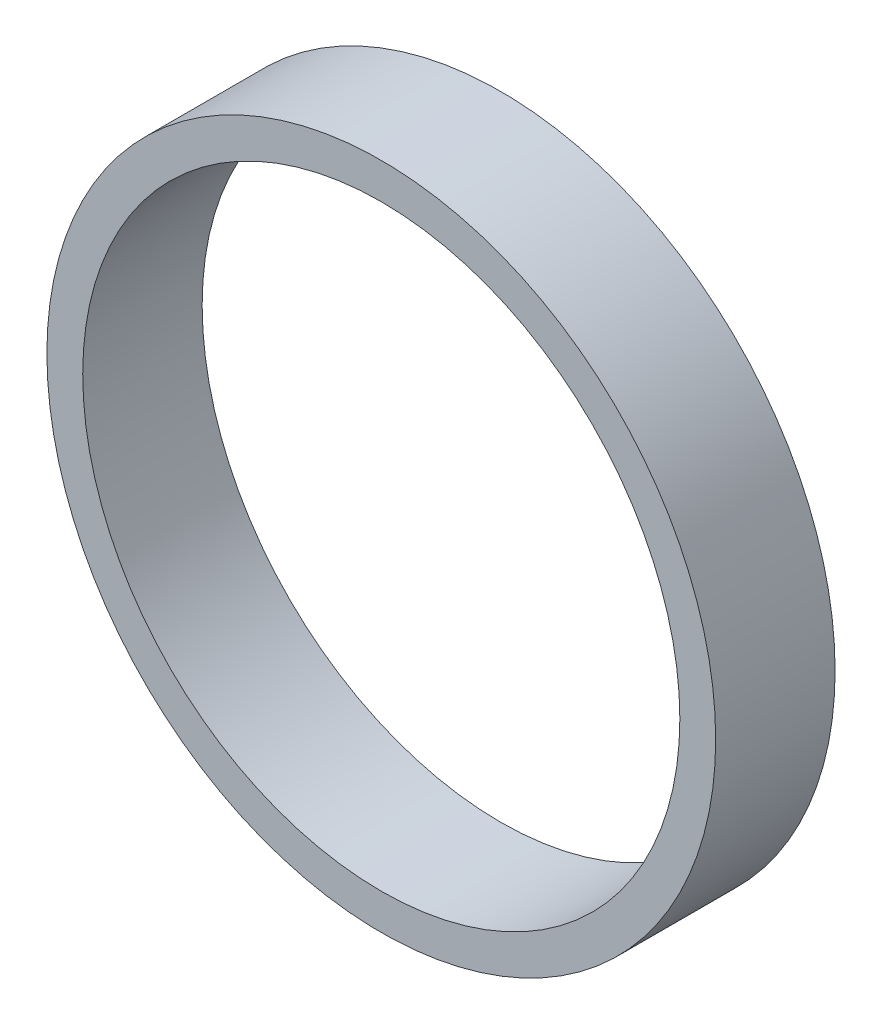
SolidWorks part; units mm, degrees
ref_plane "Front Plane" through (0, 0, 0) normal (0, 0, 1) x (1, 0, 0)
ref_plane "Top Plane" through (0, 0, 0) normal (0, 1, 0) x (1, 0, 0)
ref_plane "Right Plane" through (0, 0, 0) normal (1, 0, 0) x (0, 0, -1)
sketch "Sketch1" plane through (0, 0, 0) normal (0, 0, 1) x (1, 0, 0)
  circle A0 centre (0, 0) radius 14
  circle A1 centre (0, 0) radius 12.5
  dimension "D1" = 25
  dimension "D2" = 28
extrude "Boss-Extrude1" add sketch "Sketch1" along normal blind 5
